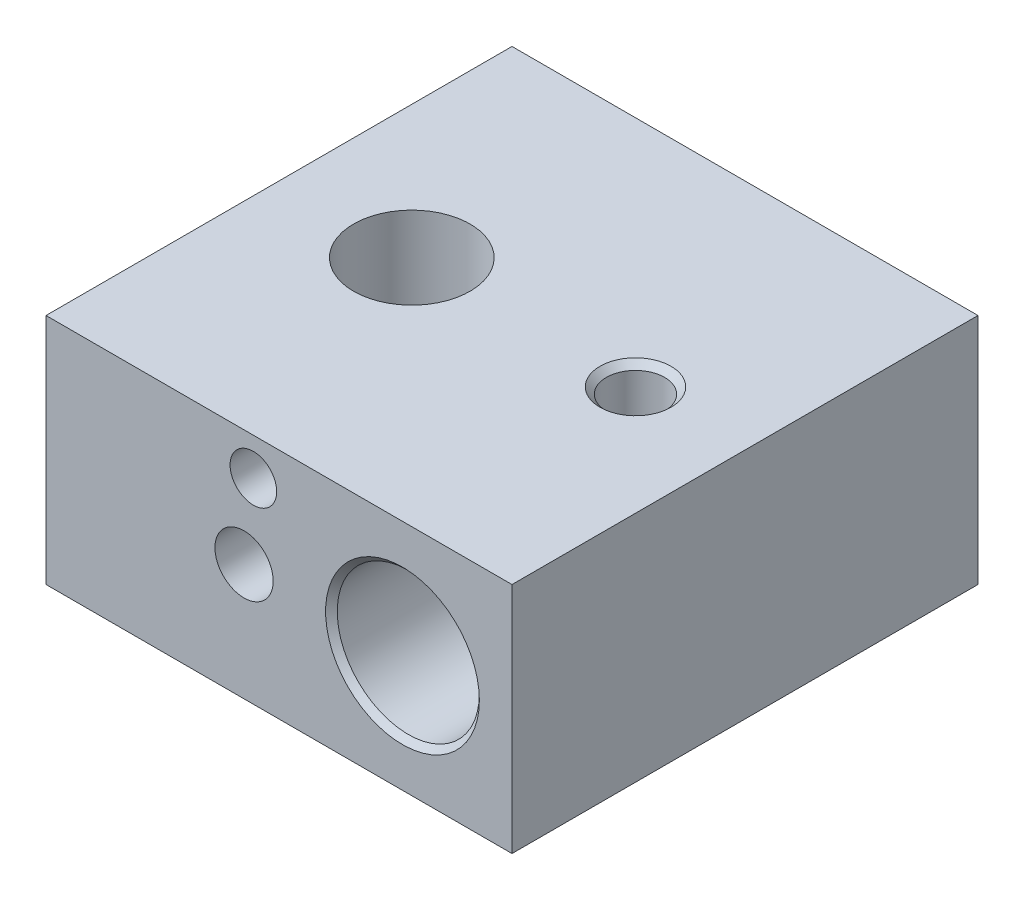
SolidWorks part; units mm, degrees
ref_plane "前视基准面" through (0, 0, 0) normal (0, 0, 1) x (1, 0, 0)
ref_plane "上视基准面" through (0, 0, 0) normal (0, 1, 0) x (1, 0, 0)
ref_plane "右视基准面" through (0, 0, 0) normal (1, 0, 0) x (0, 0, -1)
sketch "草图1" plane through (0, 0, 0) normal (0, 1, 0) x (1, 0, 0)
  line L0 (0, 0) -> (50000, 0) construction
  line L1 (10, -10) -> (-10, -10)
  line L2 (10, -10) -> (10, 10)
  line L3 (10, 10) -> (-10, 10)
  line L4 (-10, -10) -> (-10, 10)
  line L5 (0, 0) -> (0, 50000) construction
  point P0 (0, 0)
  dimension "D1" = 20
  dimension "D2" = 20
extrude "凸台-拉伸1" add sketch "草图1" along normal blind 10
sketch "草图23" plane through (0, 10, 0) normal (0, 1, 0) x (1, 0, 0)
  line L0 (-10, 10) -> (-10, -10) construction
  line L1 (-10, -10) -> (10, -10) construction
  circle A0 centre (-4.3, 0) radius 2.5
  dimension "D1" = 5
  dimension "D2" = 5.7
  dimension "D3" = 10
hole_wizard "Ø6.1 (6.1) 直径孔1" positions "草图27" profile "草图26" hole size "Ø6.1" standard "GB" end condition through all
sketch "草图27" plane through (0, 0, 10) normal (0, 0, 1) x (1, 0, 0)
  line L1 (-10, 0) -> (10, 0) construction
  line L2 (10, 10) -> (10, 0) construction
  point P0 (5.3, 5)
  dimension "D1" = 4.7
  dimension "D2" = 5
sketch "草图26" plane through (5.3, 5, 10) normal (1, 0, 0) x (0, -1, 0)
  line L0 (0, 0) -> (0, 20)
  line L1 (0, 20) -> (3.3, 20)
  line L2 (3.05, 19.75) -> (3.05, 0.25)
  line L3 (3.05, 0.25) -> (3.3, 0)
  line L5 (3.3, 0) -> (0, 0)
  line L6 (-3.05, 0.25) -> (-3.3, 0) construction
  line L7 (3.3, 20) -> (3.05, 19.75)
  line L8 (-3.3, 20) -> (-3.05, 19.75) construction
  line L11 (0, -6.35) -> (0, 107.95) construction
  dimension "通孔孔直径" = 6.1
  dimension "通孔孔深度" = 20
  dimension "近端锥形沉头孔直径" = 6.6
  dimension "近端锥形沉头孔角度" = 90
  dimension "远端锥形沉头孔直径" = 6.6
  dimension "远端锥形沉头孔角度" = 90
hole_wizard "M3 螺纹孔2" positions "草图31" profile "草图30" tap size "M3" standard "GB"
sketch "草图31" plane through (0, 0, 10) normal (0, 0, 1) x (1, 0, 0)
  line L1 (-10, 0) -> (10, 0) construction
  line L4 (5.3, 5) -> (5.3, -4.4709) construction
  point P0 (-1.5, 5)
  dimension "D1" = 6.8
  dimension "D2" = 5
sketch "草图30" plane through (-1.5, 5, 10) normal (1, 0, 0) x (0, -1, 0)
  line L0 (0, 0) -> (0, 5.7511)
  line L1 (0, 5.7511) -> (1.25, 5)
  line L2 (1.25, 5) -> (1.25, 0)
  line L5 (1.25, 0) -> (0, 0)
  line L10 (0, 5.7511) -> (-1.25, 5) construction
  line L11 (0, -6.35) -> (0, 107.95) construction
  dimension "螺纹孔钻头直径" = 2.5
  dimension "螺纹孔钻头深度" = 5
  dimension "导头角度" = 118
cosmetic thread "孔螺蚊线7" parameters "D1"=5, "D2"=3
hole_wizard "M3 螺纹孔3" positions "草图37" profile "草图36" tap size "M3" standard "GB"
sketch "草图37" plane through (0, 10, 0) normal (0, 1, 0) x (1, 0, 0)
  line L2 (0, 0) -> (50000, 0) construction
  line L3 (10, -10) -> (10, 10) construction
  point P0 (5.3, 0)
  dimension "D1" = 4.7
cosmetic thread "孔螺蚊线12" parameters "D1"=2.2179, "D2"=4
sketch "草图36" plane through (5.3, 10, 0) normal (1, 0, 0) x (0, 0, 1)
  line L0 (0, 0) -> (0, 7.25)
  line L1 (0, 7.25) -> (1.25, 6)
  line L2 (1.25, 6) -> (1.25, 0.275)
  line L3 (1.25, 0.275) -> (1.525, 0)
  line L5 (1.525, 0) -> (0, 0)
  line L6 (-1.25, 0.275) -> (-1.525, 0) construction
  line L10 (0, 7.25) -> (-1.25, 6) construction
  line L11 (0, -6.35) -> (0, 107.95) construction
  dimension "螺纹孔钻头直径" = 2.5
  dimension "螺纹孔钻头深度" = 6
  dimension "近端锥形沉头孔直径" = 3.05
  dimension "近端锥形沉头孔角度" = 90
  dimension "导头角度" = 90
extrude "切除-拉伸1" cut sketch "草图23" against normal through all
cosmetic thread "装饰螺纹线1" parameters "D2"=6
hole_wizard "打孔尺寸(%根据十字)槽半沉头木螺钉的类型1" positions "草图39" profile "草图38" countersink size "M3" standard "GB"
sketch "草图39" plane through (0, 10, 0) normal (0, 1, 0) x (1, 0, 0)
  line L0 (0, 0) -> (50000, 0) construction
  line L1 (-10, 10) -> (-10, -10) construction
  point P0 (-5.8, 6.9)
  point P2 (-5.8, -6.9)
  dimension "D1" = 13.8
  dimension "D2" = 4.2
sketch "草图38" plane through (-5.8, 10, -6.9) normal (1, 0, 0) x (0, 0, 1)
  line L0 (0, 0) -> (0, 10)
  line L1 (0, 10) -> (1.7, 10)
  line L2 (1.7, 10) -> (1.7, 1.6)
  line L3 (1.7, 1.6) -> (3.3, 0)
  line L5 (3.3, 0) -> (0, 0)
  line L6 (-1.7, 1.6) -> (-3.3, 0) construction
  line L11 (0, -6.35) -> (0, 107.95) construction
  dimension "通孔孔直径" = 3.4
  dimension "通孔孔深度" = 10
  dimension "近端锥形沉头孔直径" = 6.6
  dimension "近端锥形沉头孔角度" = 90
sketch "草图40" plane through (0, 0, 10) normal (0, 0, 1) x (1, 0, 0)
  line L0 (-10, 10) -> (10, 10) construction
  circle A0 centre (-1.1, 8.4) radius 1
  dimension "D1" = 2
  dimension "D2" = 1.6
  dimension "D3" = 1.1
extrude "切除-拉伸2" cut sketch "草图40" against normal blind 3
